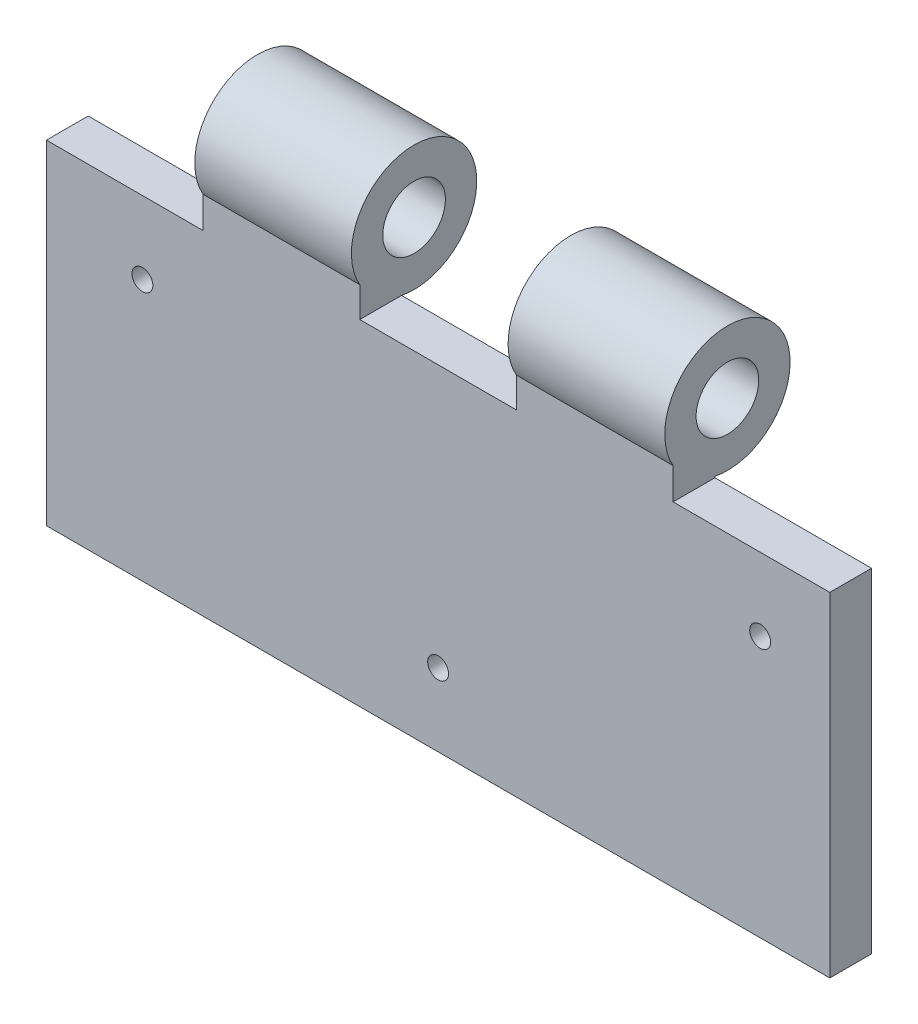
SolidWorks part; units mm, degrees
ref_plane "Front Plane" through (0, 0, 0) normal (0, 0, 1) x (1, 0, 0)
ref_plane "Top Plane" through (0, 0, 0) normal (0, 1, 0) x (1, 0, 0)
ref_plane "Right Plane" through (0, 0, 0) normal (1, 0, 0) x (0, 0, -1)
sketch "Sketch1" plane through (0, 0, 0) normal (0, 0, 1) x (1, 0, 0)
  line L1 (75, -35) -> (-75, -35)
  line L2 (75, -35) -> (75, 35)
  line L3 (75, 35) -> (-75, 35)
  line L4 (-75, -35) -> (-75, 35)
  line L5 (75, -35) -> (-75, 35) construction
  line L6 (75, 35) -> (-75, -35) construction
  point P0 (0, 0)
  dimension "D1" = 70
  dimension "D2" = 150
extrude "Boss-Extrude1" add sketch "Sketch1" along normal mid plane 8
sketch "Sketch4" plane through (75, 0, 0) normal (1, 0, 0) x (0, 0, -1)
  circle A0 centre (6.4004, 40.9538) radius 12
  circle A1 centre (6.4004, 40.9538) radius 6
  dimension "D1" = 24
  dimension "D2" = 12
sketch "Sketch7" plane through (0, 0, 4) normal (0, 0, 1) x (1, 0, 0)
  circle A0 centre (-56.6305, 15.0159) radius 2
  circle A1 centre (0, -21.0581) radius 2
  circle A2 centre (61.6697, 15.0159) radius 2
  dimension "D1" = 4
extrude "Cut-Extrude2" cut sketch "Sketch7" against normal blind 30
extrude "Boss-Extrude7" add sketch "Sketch4" against normal blind 30 from offset 30 contours A0 | A1 offset against normal yes
pattern_linear "LPattern2" count 2 spacing 60 along (-1, 0, 0) of "Boss-Extrude7"
chamfer "Chamfer3" distance 4 angle 45 3 edges at (-54.6305, 15.0159, -4) (2, -21.0581, -4) (63.6697, 15.0159, -4)
sketch "Sketch8" plane through (0, 0, 4) normal (0, 0, 1) x (1, 0, 0)
  line L1 (45, 28.9538) -> (75, 28.9538)
  line L2 (45, 28.9538) -> (45, 35)
  line L3 (45, 35) -> (75, 35)
  line L4 (75, 28.9538) -> (75, 35)
extrude "Cut-Extrude3" cut sketch "Sketch8" against normal blind 10
sketch "Sketch9" plane through (0, 0, -4) normal (0, 0, -1) x (-1, 0, 0)
  line L1 (75, 35) -> (45, 35)
  line L2 (75, 35) -> (75, 28.9538)
  line L3 (75, 28.9538) -> (45, 28.9538)
  line L4 (45, 35) -> (45, 28.9538)
extrude "Cut-Extrude4" cut sketch "Sketch9" against normal blind 10
sketch "Sketch10" plane through (0, 0, -4) normal (0, 0, -1) x (-1, 0, 0)
  line L1 (-15, 29.1963) -> (15, 29.1963)
  line L2 (-15, 29.1963) -> (-15, 35)
  line L3 (-15, 35) -> (15, 35)
  line L4 (15, 29.1963) -> (15, 35)
extrude "Cut-Extrude5" cut sketch "Sketch10" against normal blind 10
